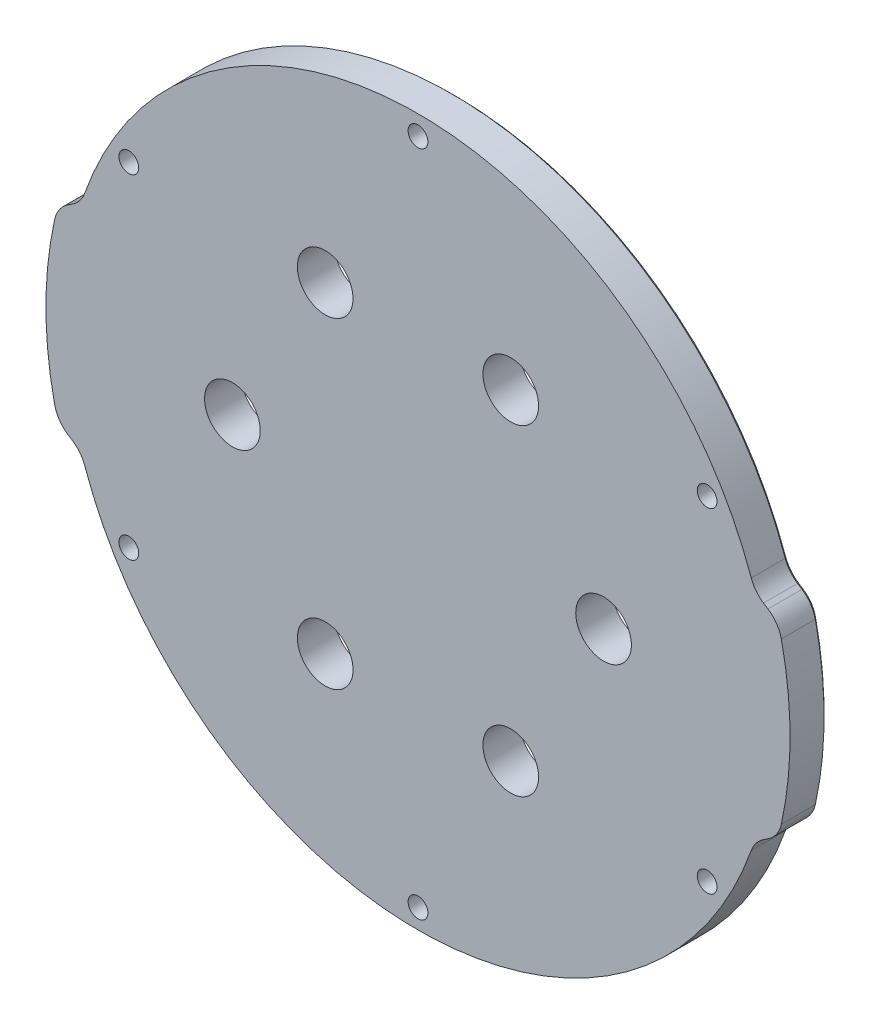
SolidWorks part; units mm, degrees
ref_plane "前视基准面" through (0, 0, 0) normal (0, 0, 1) x (1, 0, 0)
ref_plane "上视基准面" through (0, 0, 0) normal (0, 1, 0) x (1, 0, 0)
ref_plane "右视基准面" through (0, 0, 0) normal (1, 0, 0) x (0, 0, -1)
ref_plane "基准面4" through (0, 0, 6) normal (0, 0, 1) x (1, 0, 0)
sketch "草图1" plane through (0, 0, 6) normal (0, 0, 1) x (1, 0, 0)
  line L0 (-54.4047, 17.5) -> (-58.2497, 15)
  line L1 (58.2497, 15) -> (54.4047, 17.5)
  arc A0 (-58.2497, 15) -> (58.2497, 15) centre (0, 0) ccw
  arc A1 (54.4047, 17.5) -> (-54.4047, 17.5) centre (0, 0) ccw
extrude "凸台-拉伸1" add sketch "草图1" against normal blind 6
sketch "草图2" plane through (0, 0, 0) normal (0, 0, -1) x (-1, 0, 0)
  line L0 (58.2497, -15) -> (54.4047, -17.5)
  line L1 (-54.4047, -17.5) -> (-58.2497, -15)
  arc A0 (54.4047, -17.5) -> (-54.4047, -17.5) centre (0, 0) cw
  arc A1 (-58.2497, -15) -> (58.2497, -15) centre (0, 0) ccw
extrude "切除-拉伸1" cut sketch "草图2" against normal through all
hole_wizard "Ø9.0 (9) 直径孔1" positions "草图4" profile "草图3" hole size "Ø9.0" standard "ANSI Metric"
sketch "草图4" plane through (0, 0, 0) normal (0, 0, -1) x (-1, 0, 0)
  point P0 (-15, 25.9808)
  point P1 (15, 25.9808)
  point P2 (30, 0)
  point P3 (15, -25.9808)
  point P4 (-15, -25.9808)
  point P5 (-30, 0)
sketch "草图3" plane through (15, 25.9808, 0) normal (1, 0, 0) x (0, 1, 0)
  line L0 (0, 0) -> (0, 6)
  line L1 (0, 6) -> (4.5, 6)
  line L2 (4.5, 6) -> (4.5, 0)
  line L5 (4.5, 0) -> (0, 0)
  line L11 (0, -6.35) -> (0, 107.95) construction
  dimension "通孔孔直径" = 9
  dimension "通孔孔深度" = 6
hole_wizard "Ø3.2 (3.2) 直径孔1" positions "草图6" profile "草图5" hole size "Ø3.2" standard "ANSI Metric"
sketch "草图6" plane through (0, 0, 0) normal (0, 0, -1) x (-1, 0, 0)
  point P0 (0, 53.975)
  point P1 (46.7437, -26.9875)
  point P2 (-46.7437, 26.9875)
  point P3 (-46.7437, -26.9875)
  point P4 (0, -53.975)
  point P5 (46.7437, 26.9875)
sketch "草图5" plane through (0, 53.975, 0) normal (1, 0, 0) x (0, 1, 0)
  line L0 (0, 0) -> (0, 6)
  line L1 (0, 6) -> (1.6, 6)
  line L2 (1.6, 6) -> (1.6, 0)
  line L5 (1.6, 0) -> (0, 0)
  line L11 (0, -6.35) -> (0, 107.95) construction
  dimension "通孔孔直径" = 3.2
  dimension "通孔孔深度" = 6
fillet "圆角1" radius 5 8 edges at (-54.4047, -17.5, 3) (58.2497, 15, 3) (54.4047, -17.5, 3) (-58.2497, -15, 3) (54.4047, 17.5, 3) (-54.4047, 17.5, 3) (58.2497, -15, 3) (-58.2497, 15, 3)
chamfer "倒角1" distance 0.5 angle 45 16 edges at (0, 57.15, 0) (54.6578, 17.6514, 0) (-54.6578, 17.6514, 0) (56.2186, 16.3206, 0) (-56.2186, 16.3206, 0) (57.962, 14.7428, 0) (-57.962, 14.7428, 0) (60.15, 0, 0) (-60.15, 0, 0) (57.962, -14.7428, 0) (-57.962, -14.7428, 0) (56.2186, -16.3206, 0) (-56.2186, -16.3206, 0) (54.6578, -17.6514, 0) (-54.6578, -17.6514, 0) (0, -57.15, 0)
